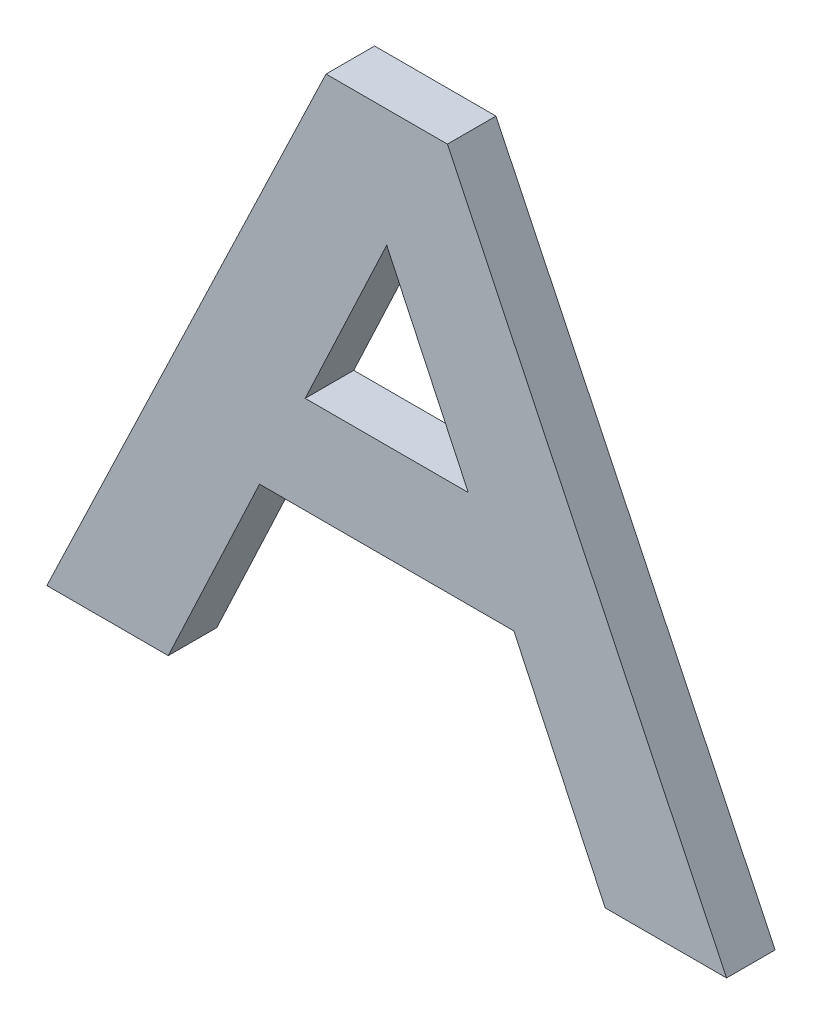
SolidWorks part; units mm, degrees
ref_plane "Front Plane" through (0, 0, 0) normal (0, 0, 1) x (1, 0, 0)
ref_plane "Top Plane" through (0, 0, 0) normal (0, 1, 0) x (1, 0, 0)
ref_plane "Right Plane" through (0, 0, 0) normal (1, 0, 0) x (0, 0, -1)
sketch "Sketch1" plane through (0, 0, 0) normal (0, 0, 1) x (1, 0, 0)
  line L0 (0, 76.2) -> (0, 0)
  line L1 (-7.9375, 76.2) -> (7.9375, 76.2)
  line L2 (7.9375, 76.2) -> (44.45, 0)
  line L3 (44.45, 0) -> (28.575, 0)
  line L11 (-44.45, 0) -> (-28.575, 0)
  line L13 (-7.9375, 76.2) -> (-44.45, 0)
  line L16 (-28.575, 0) -> (-16.6346, 25.4)
  line L17 (-16.6346, 25.4) -> (16.6346, 25.4)
  line L18 (0, 25.4) -> (0, 38.1)
  line L19 (10.6644, 38.1) -> (-10.6644, 38.1)
  line L20 (-10.6644, 38.1) -> (0, 60.7855)
  line L21 (28.575, 0) -> (16.6346, 25.4)
  line L22 (10.6644, 38.1) -> (0, 60.7855)
  point P11 (-36.5125, 0)
  point P17 (0, 76.2)
  dimension "D1" = 76.2
  dimension "D2" = 12.7
  dimension "D3" = 25.4
  dimension "D4" = 15.875
  dimension "D5" = 15.875
  dimension "D6" = 15.875
  dimension "D7" = 25.4
extrude "Boss-Extrude3" add sketch "Sketch1" along normal blind 6.35 contours L19 L20 L0 L1 L13 L11 L16 L17 | L22 L19 L0 L17 L21 L3 L2 L1
